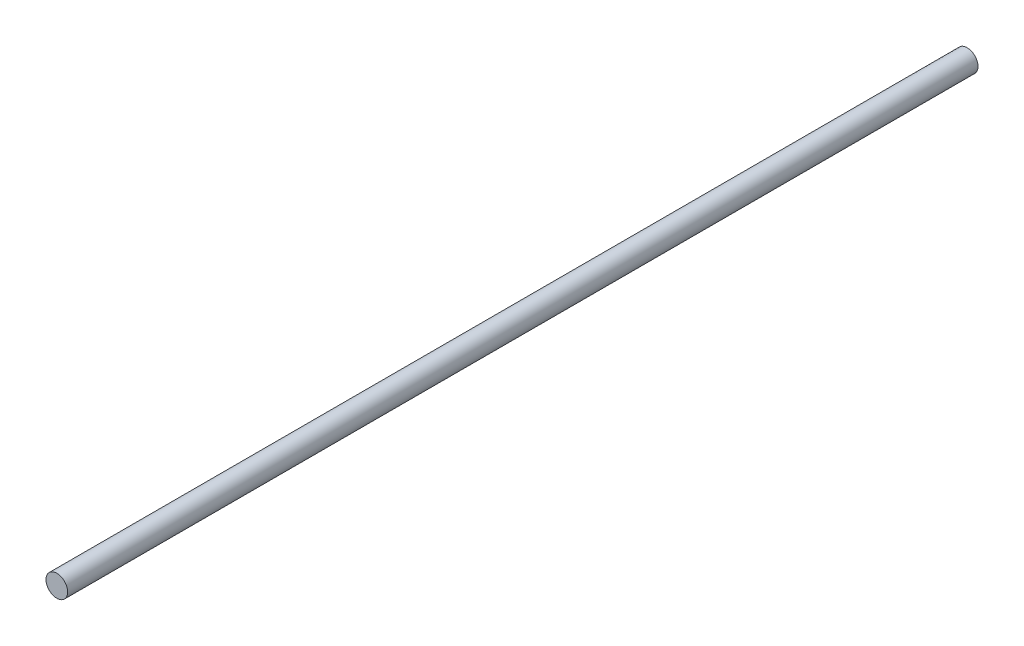
SolidWorks part; units mm, degrees
ref_plane "Front" through (0, 0, 0) normal (0, 0, 1) x (1, 0, 0)
ref_plane "Top" through (0, 0, 0) normal (0, 1, 0) x (1, 0, 0)
ref_plane "Right" through (0, 0, 0) normal (1, 0, 0) x (0, 0, -1)
sketch "Sketch1" plane through (0, 0, 0) normal (0, 0, 1) x (1, 0, 0)
  circle A0 centre (0, 0) radius 3.175
  dimension "D1" = 6.35
extrude "Extrude1" add sketch "Sketch1" along normal mid plane 266.7
chamfer "Chamfer1" [suppressed] distance 0.635 angle 45
equation "\"D1@Chamfer1\" = \"D1@Sketch1\" * .1"
